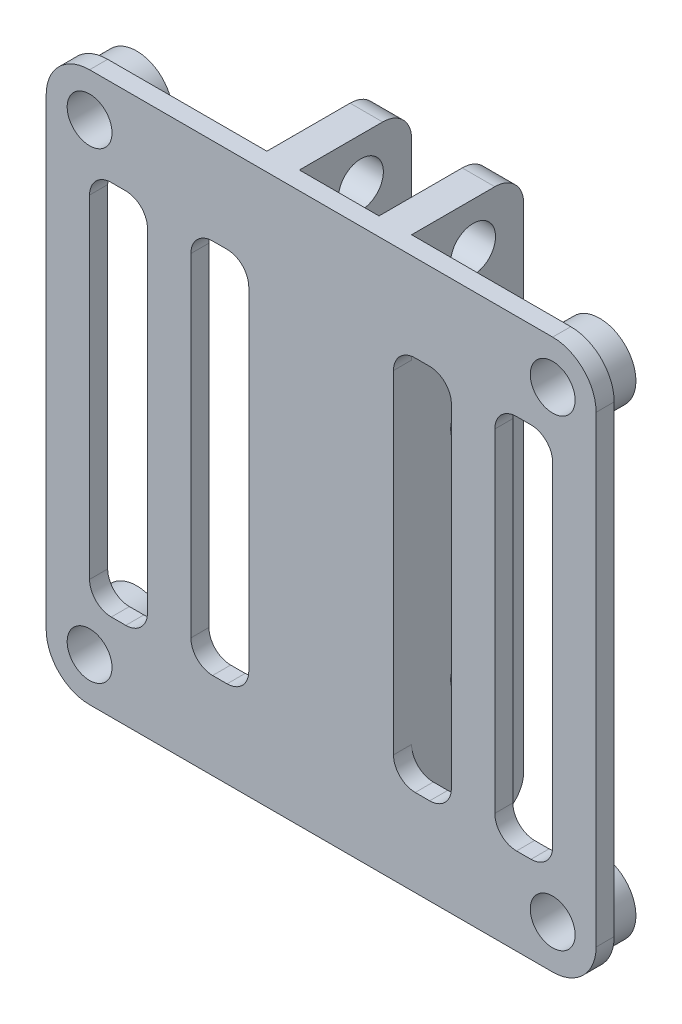
SolidWorks part; units mm, degrees
ref_plane "Plan de face" through (0, 0, 0) normal (0, 0, 1) x (1, 0, 0)
ref_plane "Plan de dessus" through (0, 0, 0) normal (0, 1, 0) x (1, 0, 0)
ref_plane "Plan de droite" through (0, 0, 0) normal (1, 0, 0) x (0, 0, -1)
sketch "Esquisse1" plane through (0, 0, 0) normal (0, 0, 1) x (1, 0, 0)
  line L1 (0, 0) -> (38, 0)
  line L2 (0, 0) -> (0, 38)
  line L3 (0, 38) -> (38, 38)
  line L4 (38, 0) -> (38, 38)
  point P4 (0, 0)
  point P5 (0, 0)
extrude "Boss.-Extru.1" add sketch "Esquisse1" along normal blind 9
sketch "Esquisse2" plane through (0, 0, 0) normal (0, 0, -1) x (-1, 0, 0)
  line L1 (-14, 38) -> (0, 38)
  line L2 (-14, 38) -> (-14, 0)
  line L3 (-14, 0) -> (0, 0)
  line L4 (0, 38) -> (0, 0)
  line L5 (-38, 38) -> (-24, 38)
  line L6 (-38, 38) -> (-38, 0)
  line L7 (-38, 0) -> (-24, 0)
  line L8 (-24, 38) -> (-24, 0)
  line L9 (-16.25, 38) -> (-21.75, 38)
  line L10 (-16.25, 38) -> (-16.25, 0)
  line L11 (-16.25, 0) -> (-21.75, 0)
  line L12 (-21.75, 38) -> (-21.75, 0)
  point P12 (0, 0)
  point P13 (0, 0)
  point P14 (0, 0)
  point P15 (0, 0)
  point P16 (0, 0)
  point P17 (0, 0)
  point P18 (0, 0)
  point P19 (0, 0)
  point P20 (0, 0)
  point P21 (0, 0)
  point P22 (0, 0)
  point P23 (0, 0)
extrude "Enlèv. mat.-Extru.1" cut sketch "Esquisse2" against normal blind 7.75
sketch "Esquisse3" plane through (24, 0, 0) normal (1, 0, 0) x (0, 0, -1)
  circle A0 centre (-3.5, 10) radius 1.55
  circle A1 centre (-3.5, 35) radius 1.55
  circle A2 centre (-3.5, 25) radius 1.55
  point P2 (0, 0)
  point P5 (0, 0)
  point P6 (0, 0)
  point P9 (-3.0817, 25.7157)
  point P10 (0, 0)
extrude "Enlèv. mat.-Extru.2" cut sketch "Esquisse3" against normal through all
fillet "Congé1" radius 3 4 edges at (0, 0, 8.375) (38, 0, 8.375) (0, 38, 8.375) (38, 38, 8.375)
sketch "Esquisse9" plane through (0, 0, 7.75) normal (0, 0, -1) x (-1, 0, 0)
  circle A1 centre (-35, 35) radius 2.5
  circle A2 centre (-3, 35) radius 2.5
  circle A3 centre (-3, 3) radius 2.5
  circle A4 centre (-35, 3) radius 2.5
  point P8 (0, 0)
  point P9 (0, 0)
  point P10 (0, 0)
  point P11 (0, 0)
  point P12 (0, 0)
fillet "Congé2" radius 2 4 edges at (22.875, 0, 0) (15.125, 0, 0) (15.125, 38, 0) (22.875, 38, 0)
extrude "Boss.-Extru.2" add sketch "Esquisse9" along normal blind 2
sketch "Esquisse5" plane through (0, 0, 7.75) normal (0, 0, -1) x (-1, 0, 0)
  circle A0 centre (-35, 35) radius 1.55
  circle A1 centre (-35, 3) radius 1.55
  circle A2 centre (-3, 3) radius 1.55
  circle A3 centre (-3, 35) radius 1.55
  point P8 (0, 0)
  point P9 (0, 0)
  point P10 (0, 0)
  point P11 (0, 0)
  point P12 (0, 0)
  point P13 (0, 0)
  point P14 (0, 0)
  point P15 (0, 0)
  point P16 (0, 0)
  point P17 (0, 0)
  point P18 (0, 0)
  point P19 (0, 0)
  point P20 (0, 0)
  point P21 (0, 0)
extrude "Enlèv. mat.-Extru.4" cut sketch "Esquisse5" against normal through all both and the other way through all
sketch "Esquisse10" plane through (0, 0, 9) normal (0, 0, 1) x (1, 0, 0)
  line L0 (10, 32) -> (14, 32)
  line L1 (3, 32) -> (7, 32)
  line L2 (3, 32) -> (3, 6)
  line L3 (3, 6) -> (7, 6)
  line L4 (7, 32) -> (7, 6)
  line L5 (10, 32) -> (10, 6)
  line L6 (14, 32) -> (14, 6)
  line L7 (10, 6) -> (14, 6)
  line L8 (28, 32) -> (28, 6)
  line L9 (35, 32) -> (31, 32)
  line L10 (35, 32) -> (35, 6)
  line L11 (35, 6) -> (31, 6)
  line L12 (31, 32) -> (31, 6)
  line L13 (28, 32) -> (24, 32)
  line L14 (24, 32) -> (24, 6)
  line L15 (28, 6) -> (24, 6)
  dimension "D1" = 2
  dimension "D2" = 2
extrude "Enlèv. mat.-Extru.5" cut sketch "Esquisse10" against normal through all
fillet "Congé3" radius 1.5 16 edges at (24, 32, 8.375) (31, 32, 8.375) (35, 32, 8.375) (28, 32, 8.375) (14, 32, 8.375) (7, 32, 8.375) (10, 32, 8.375) (3, 32, 8.375) (7, 6, 8.375) (14, 6, 8.375) (28, 6, 8.375) (35, 6, 8.375) (31, 6, 8.375) (24, 6, 8.375) (10, 6, 8.375) (3, 6, 8.375)
